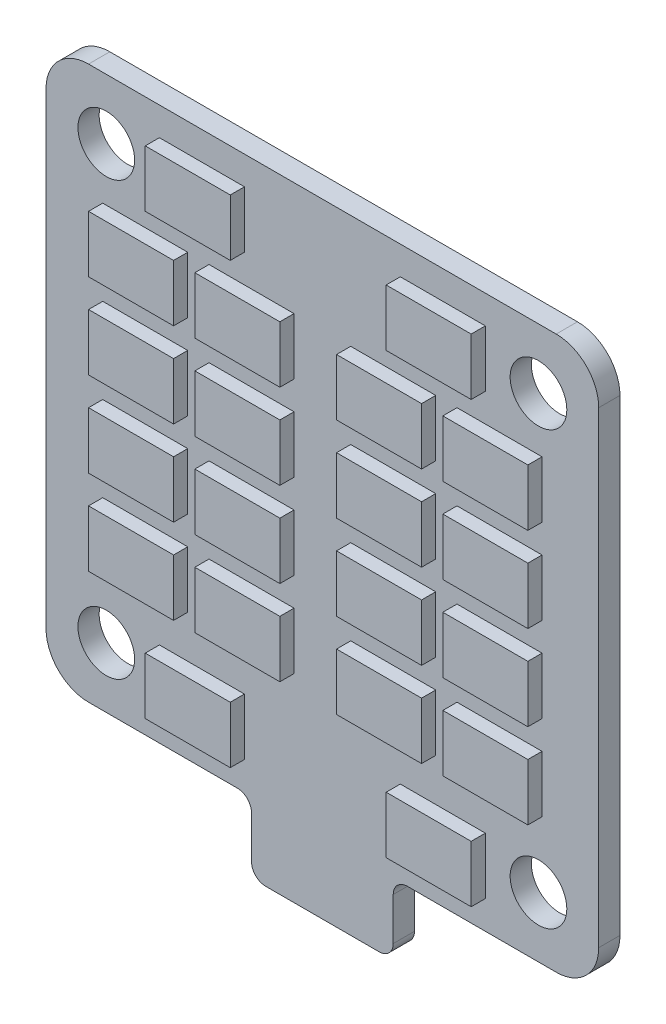
SolidWorks part; units mm, degrees
ref_plane "Front Plane" through (0, 0, 0) normal (0, 0, 1) x (1, 0, 0)
ref_plane "Top Plane" through (0, 0, 0) normal (0, 1, 0) x (1, 0, 0)
ref_plane "Right Plane" through (0, 0, 0) normal (1, 0, 0) x (0, 0, -1)
sketch "Sketch2" plane through (0, 0, 0) normal (0, 0, 1) x (1, 0, 0)
  line L1 (-16.5, -19.5) -> (-6, -19.5)
  line L2 (-19.5, -16.5) -> (-19.5, 16.5)
  line L3 (-16.5, 19.5) -> (16.5, 19.5)
  line L4 (19.5, -16.5) -> (19.5, 16.5)
  line L5 (-19.5, -19.5) -> (19.5, 19.5) construction
  line L6 (-19.5, 19.5) -> (19.5, -19.5) construction
  line L7 (-5, -20.5) -> (-5, -23.5)
  line L8 (5, -20.5) -> (5, -23.5)
  line L9 (-4, -24.5) -> (4, -24.5)
  line L10 (6, -19.5) -> (16.5, -19.5)
  circle A0 centre (15.25, 15.25) radius 2
  circle A1 centre (15.25, -15.25) radius 2
  circle A2 centre (-15.25, -15.25) radius 2
  circle A3 centre (-15.25, 15.25) radius 2
  arc A4 (19.5, 16.5) -> (16.5, 19.5) centre (16.5, 16.5) ccw
  arc A5 (16.5, -19.5) -> (19.5, -16.5) centre (16.5, -16.5) ccw
  arc A6 (-16.5, -19.5) -> (-19.5, -16.5) centre (-16.5, -16.5) cw
  arc A7 (-19.5, 16.5) -> (-16.5, 19.5) centre (-16.5, 16.5) cw
  arc A8 (6, -19.5) -> (5, -20.5) centre (6, -20.5) ccw
  arc A9 (5, -23.5) -> (4, -24.5) centre (4, -23.5) cw
  arc A10 (-4, -24.5) -> (-5, -23.5) centre (-4, -23.5) cw
  arc A11 (-5, -20.5) -> (-6, -19.5) centre (-6, -20.5) ccw
  point P0 (0, 0)
  point P32 (5, -19.5)
  point P35 (5, -24.5)
  point P38 (-5, -24.5)
  dimension "D3" = 4
  dimension "D6" = 3
  dimension "D10" = 1
  dimension "D1" = 39
  dimension "D2" = 39
  dimension "D4" = 15.25
  dimension "D7" = 10
  dimension "D8" = 5
  dimension "D9" = 5
  dimension "D5" = 4
extrude "Boss-Extrude1" add sketch "Sketch2" along normal blind 1.5
sketch "Sketch3" plane through (0, 0, 1.5) normal (0, 0, 1) x (1, 0, 0)
  line L0 (0, 19.5) -> (0, -24.5) construction
  line L1 (16.5, 19.5) -> (-16.5, 19.5) construction
  line L2 (-4, -24.5) -> (4, -24.5) construction
  line L3 (-8, 5.5) -> (-8, 1.5)
  line L4 (-8, 11.5) -> (-2, 11.5)
  line L5 (-8, 11.5) -> (-8, 7.5)
  line L6 (-8, 7.5) -> (-2, 7.5)
  line L7 (-2, 11.5) -> (-2, 7.5)
  line L8 (-8, 11.5) -> (-2, 7.5) construction
  line L9 (-8, 7.5) -> (-2, 11.5) construction
  line L10 (-8, 5.5) -> (-2, 5.5)
  line L11 (-2, 5.5) -> (-2, 1.5)
  line L12 (-8, 1.5) -> (-2, 1.5)
  line L13 (-8, -0.5) -> (-8, -4.5)
  line L14 (-8, -0.5) -> (-2, -0.5)
  line L15 (-2, -0.5) -> (-2, -4.5)
  line L16 (-8, -4.5) -> (-2, -4.5)
  line L17 (-8, -6.5) -> (-8, -10.5)
  line L18 (-8, -6.5) -> (-2, -6.5)
  line L19 (-2, -6.5) -> (-2, -10.5)
  line L20 (-8, -10.5) -> (-2, -10.5)
  line L21 (-15.5, 11.5) -> (-15.5, 7.5)
  line L22 (-15.5, 11.5) -> (-9.5, 11.5)
  line L23 (-9.5, 11.5) -> (-9.5, 7.5)
  line L24 (-15.5, 7.5) -> (-9.5, 7.5)
  line L25 (-15.5, 5.5) -> (-15.5, 1.5)
  line L26 (-15.5, 1.5) -> (-9.5, 1.5)
  line L27 (-9.5, 5.5) -> (-9.5, 1.5)
  line L28 (-15.5, 5.5) -> (-9.5, 5.5)
  line L29 (-15.5, -0.5) -> (-15.5, -4.5)
  line L30 (-15.5, -4.5) -> (-9.5, -4.5)
  line L31 (-9.5, -0.5) -> (-9.5, -4.5)
  line L32 (-15.5, -0.5) -> (-9.5, -0.5)
  line L33 (-15.5, -6.5) -> (-15.5, -10.5)
  line L34 (-15.5, -10.5) -> (-9.5, -10.5)
  line L35 (-9.5, -6.5) -> (-9.5, -10.5)
  line L36 (-15.5, -6.5) -> (-9.5, -6.5)
  line L37 (15.5, -6.5) -> (9.5, -6.5)
  line L38 (9.5, -6.5) -> (9.5, -10.5)
  line L39 (15.5, -10.5) -> (9.5, -10.5)
  line L40 (15.5, -6.5) -> (15.5, -10.5)
  line L41 (15.5, -0.5) -> (9.5, -0.5)
  line L42 (9.5, -0.5) -> (9.5, -4.5)
  line L43 (15.5, -4.5) -> (9.5, -4.5)
  line L44 (15.5, -0.5) -> (15.5, -4.5)
  line L45 (15.5, 5.5) -> (9.5, 5.5)
  line L46 (9.5, 5.5) -> (9.5, 1.5)
  line L47 (15.5, 1.5) -> (9.5, 1.5)
  line L48 (15.5, 5.5) -> (15.5, 1.5)
  line L49 (15.5, 11.5) -> (9.5, 11.5)
  line L50 (9.5, 11.5) -> (9.5, 7.5)
  line L51 (15.5, 7.5) -> (9.5, 7.5)
  line L52 (15.5, 11.5) -> (15.5, 7.5)
  line L53 (8, -6.5) -> (2, -6.5)
  line L54 (2, -6.5) -> (2, -10.5)
  line L55 (8, -10.5) -> (2, -10.5)
  line L56 (8, -6.5) -> (8, -10.5)
  line L57 (8, -0.5) -> (2, -0.5)
  line L58 (2, -0.5) -> (2, -4.5)
  line L59 (8, -4.5) -> (2, -4.5)
  line L60 (8, -0.5) -> (8, -4.5)
  line L61 (8, 5.5) -> (2, 5.5)
  line L62 (2, 5.5) -> (2, 1.5)
  line L63 (8, 1.5) -> (2, 1.5)
  line L64 (8, 5.5) -> (8, 1.5)
  line L65 (8, 7.5) -> (2, 7.5)
  line L66 (2, 11.5) -> (2, 7.5)
  line L67 (8, 11.5) -> (2, 11.5)
  line L68 (8, 11.5) -> (8, 7.5)
  line L69 (11.5, 13.5) -> (5.5, 13.5)
  line L70 (-11.5, 17.5) -> (-5.5, 17.5)
  line L71 (-11.5, 17.5) -> (-11.5, 13.5)
  line L72 (-11.5, 13.5) -> (-5.5, 13.5)
  line L73 (-5.5, 17.5) -> (-5.5, 13.5)
  line L74 (-11.5, 17.5) -> (-5.5, 13.5) construction
  line L75 (-11.5, 13.5) -> (-5.5, 17.5) construction
  line L76 (5.5, 17.5) -> (5.5, 13.5)
  line L77 (11.5, 17.5) -> (5.5, 17.5)
  line L78 (11.5, 17.5) -> (11.5, 13.5)
  line L79 (-19.5, 0) -> (19.5, 0) construction
  line L80 (-19.5, 16.5) -> (-19.5, -16.5) construction
  line L81 (19.5, -16.5) -> (19.5, 16.5) construction
  line L82 (11.5, -17.5) -> (11.5, -13.5)
  line L83 (11.5, -17.5) -> (5.5, -17.5)
  line L84 (5.5, -17.5) -> (5.5, -13.5)
  line L85 (11.5, -13.5) -> (5.5, -13.5)
  line L86 (-11.5, -13.5) -> (-5.5, -13.5)
  line L87 (-5.5, -17.5) -> (-5.5, -13.5)
  line L88 (-11.5, -17.5) -> (-5.5, -17.5)
  line L89 (-11.5, -17.5) -> (-11.5, -13.5)
  point P6 (-5, 9.5)
  point P71 (-8.5, 15.5)
  dimension "D1" = 4
  dimension "D2" = 6
  dimension "D3" = 5
  dimension "D4" = 10
  dimension "D7" = 6
  dimension "D8" = 4
  dimension "D9" = 8.5
  dimension "D10" = 4
  dimension "D5" = 4
  dimension "D6" = 2
extrude "Boss-Extrude2" add sketch "Sketch3" along normal blind 1
